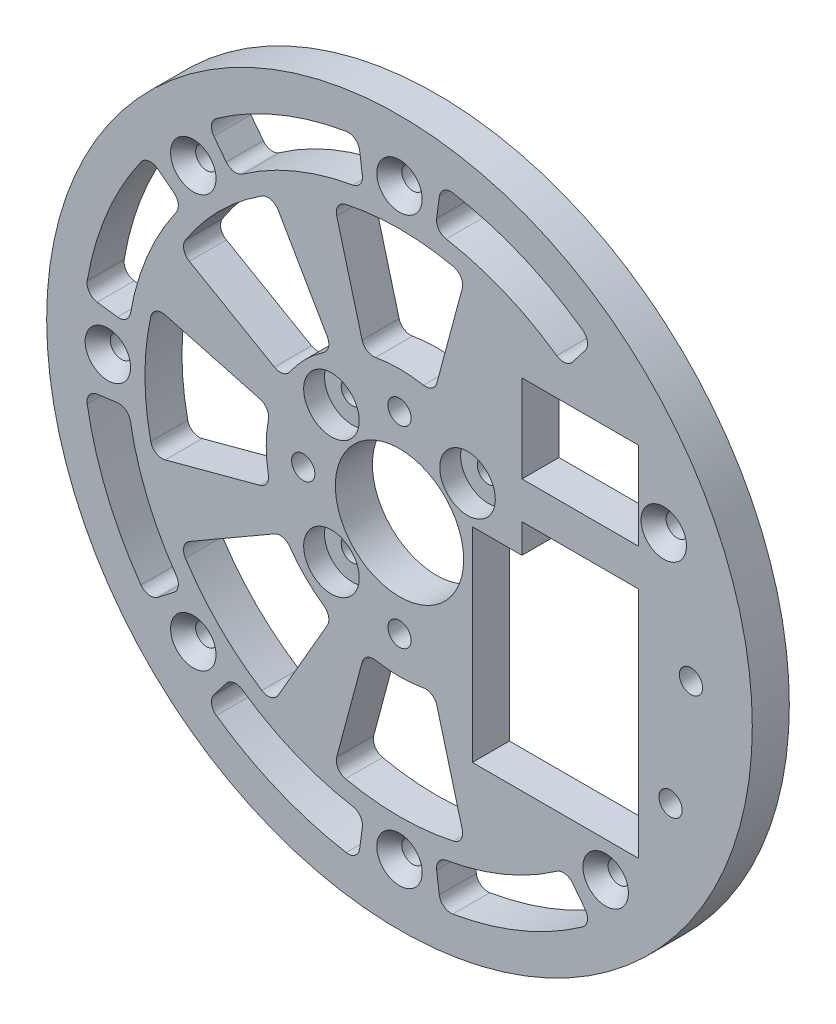
SolidWorks part; units mm, degrees
material "Balsa"
ref_plane "Front Plane" through (0, 0, 0) normal (0, 0, 1) x (1, 0, 0)
ref_plane "Top Plane" through (0, 0, 0) normal (0, 1, 0) x (1, 0, 0)
ref_plane "Right Plane" through (0, 0, 0) normal (1, 0, 0) x (0, 0, -1)
sketch "Sketch1" plane through (0, 0, 0) normal (0, 0, 1) x (1, 0, 0)
  line L0 (45.3154, 21.1309) -> (0, 0) construction
  line L1 (0, 0) -> (35.3553, -35.3553) construction
  line L2 (49.9788, 1.4542) -> (0, 0) construction
  line L3 (0, 0) -> (46.4674, -18.4603) construction
  circle A0 centre (45.3154, 21.1309) radius 1.8986
  circle A1 centre (49.9788, 1.4542) radius 1.9939
  circle A2 centre (0, 0) radius 60.5
  circle A3 centre (0, 0) radius 11
  circle A4 centre (0, 0) radius 16.5 construction
  circle A5 centre (46.4674, -18.4603) radius 1.9939
  circle A6 centre (0, 0) radius 50 construction
  circle A27 centre (0, -16.5) radius 1.9939
  circle A28 centre (11.6673, -11.6673) radius 1.8986 construction
  circle A30 centre (0, -50) radius 1.8986
  circle A31 centre (-16.5, 0) radius 1.9939
  circle A32 centre (-11.6673, -11.6673) radius 1.8986
  circle A33 centre (0, 16.5) radius 1.9939
  circle A34 centre (-11.6673, 11.6673) radius 1.8986
  circle A35 centre (16.5, 0) radius 1.9939 construction
  circle A36 centre (11.6673, 11.6673) radius 1.8986
  circle A38 centre (-35.3553, -35.3553) radius 1.8986
  circle A40 centre (-50, 0) radius 1.8986
  circle A42 centre (-35.3553, 35.3553) radius 1.8986
  circle A44 centre (0, 50) radius 1.8986
  circle A46 centre (35.3553, 35.3553) radius 1.8986 construction
  circle A48 centre (50, 0) radius 1.8986 construction
  circle A50 centre (35.3553, -35.3553) radius 1.8986
  point P72 (0, 0)
  dimension "D1" = 121
  dimension "D4" = 70
  dimension "D6" = 100
  dimension "D7" = 23.333
  dimension "D8" = 33
  dimension "D9" = 3.7973
  dimension "D10" = 3.9878
  dimension "D15" = 3.7973
  dimension "D17" = 3.9878
  dimension "D18" = 3.7973
  dimension "D3" = 22
  dimension "D11" = 3.9878
  dimension "D5" = 23.333
  dimension "D19" = 45
  dimension "D20" = 4
  dimension "D21" = 8
extrude "Boss-Extrude1" add sketch "Sketch1" along normal blind 6.35
sketch "Sketch2" plane through (0, 0, 0) normal (0, 0, 1) x (1, 0, 0)
  line L0 (12.5, -29.35) -> (41, -29.35)
  line L1 (41, -29.35) -> (41, 10.65)
  line L5 (41, 17) -> (41, 32)
  line L6 (41, 32) -> (21, 32)
  line L7 (21, 32) -> (21, 17)
  line L8 (21, 17) -> (41, 17)
  line L10 (41, 10.65) -> (21, 10.65)
  line L11 (21, 10.65) -> (21, 5.65)
  line L12 (21, 5.65) -> (12.5, 5.65)
  line L13 (12.5, 5.65) -> (12.5, -29.35)
  dimension "D1" = 20
  dimension "D2" = 6.35
  dimension "D3" = 40
  dimension "D4" = 15
  dimension "D6" = 5
  dimension "D8" = 8.5
  dimension "D9" = 21
  dimension "D10" = 32
extrude "Cut-Extrude1" cut sketch "Sketch2" along normal through all
sketch "Sketch3" plane through (0, 0, 6.35) normal (0, 0, 1) x (1, 0, 0)
  line L0 (0, 0) -> (-84.2283, 0) construction
  line L4 (-42.1627, -11.2975) -> (-22.0714, -5.914)
  line L5 (-22.0714, 5.914) -> (-42.1627, 11.2975)
  arc A0 (-42.1627, -11.2975) -> (-42.1627, 11.2975) centre (0, 0) cw
  arc A1 (-22.0714, -5.914) -> (-22.0714, 5.914) centre (0, 0) cw
  circle A2 centre (-16.5, 0) radius 1.9939 construction
  circle A4 centre (-50, 0) radius 1.8987 construction
  circle A5 centre (-50, 0) radius 1.8986 construction
  point P6 (-43.65, 0)
  point P7 (-22.85, 0)
  dimension "D1" = 6.35
  dimension "D3" = 30
  dimension "D2" = 6.35
extrude "Cut-Extrude2" cut sketch "Sketch3" against normal through all
fillet "Fillet1" radius 2 4 edges at (-42.1627, -11.2975, 3.175) (-22.0714, -5.914, 3.175) (-22.0714, 5.914, 3.175) (-42.1627, 11.2975, 3.175)
pattern_circular "CirPattern1" count 8 over 360 about axis through (0, 0, 0) along (0, 0, 1) skipping 3, 4, 5 of "Fillet1", "Cut-Extrude2"
sketch "Sketch4" plane through (0, 0, 6.35) normal (0, 0, 1) x (1, 0, 0)
  line L0 (-85.2293, 0) -> (0, 0) construction
  line L1 (0, 0) -> (-89.0309, 36.8778) construction
  line L2 (-43.0989, 33.071) -> (-37.1488, 28.5053)
  line L3 (-53.8602, 7.0908) -> (-46.4244, 6.1119)
  arc A0 (-46.4244, 6.1119) -> (-37.1488, 28.5053) centre (0, 0) cw
  arc A1 (-53.8602, 7.0908) -> (-43.0989, 33.071) centre (0, 0) cw
  circle A2 centre (-50, 0) radius 1.8987 construction
  circle A3 centre (-50, 0) radius 1.8986
  arc A4 (-42.6565, 9.2598) -> (-42.6565, -9.2598) centre (0, 0) ccw construction
  circle A5 centre (0, 0) radius 60.5 construction
  point P17 (-43.2607, 17.9192)
  dimension "D3" = 3.175
  dimension "D4" = 6.175
  dimension "D1" = 22.5
  dimension "D2" = 30
extrude "Cut-Extrude3" cut sketch "Sketch4" against normal through all
fillet "Fillet2" radius 2 4 edges at (-53.8602, 7.0908, 3.175) (-46.4244, 6.1119, 3.175) (-37.1488, 28.5053, 3.175) (-43.0989, 33.071, 3.175)
pattern_circular "CirPattern2" count 8 over 360 about axis through (0, 0, 0) along (0, 0, 1) skipping 3, 4 of "Fillet2", "Cut-Extrude3"
chamfer "Chamfer1" distance 2.301 angle 41 7 edges at (1.8986, 50, 6.35) (-33.4567, 35.3553, 6.35) (-48.1014, 0, 6.35) (-33.4567, -35.3553, 6.35) (1.8986, -50, 6.35) (37.254, -35.3553, 6.35) (47.214, 21.1309, 6.35)
sketch "Sketch5" plane through (0, 0, 6.35) normal (0, 0, 1) x (1, 0, 0)
  circle A0 centre (-11.6673, -11.6673) radius 1.8986 construction
  circle A1 centre (-11.6673, 11.6673) radius 1.8986 construction
  circle A2 centre (11.6673, 11.6673) radius 1.8986 construction
  circle A3 centre (-11.6673, -11.6673) radius 1.8986
  circle A4 centre (-11.6673, 11.6673) radius 1.8986
  circle A5 centre (11.6673, 11.6673) radius 1.8986
  circle A6 centre (11.6673, 11.6673) radius 4.7625
  circle A7 centre (-11.6673, 11.6673) radius 4.7625
  circle A8 centre (-11.6673, -11.6673) radius 4.7625
  dimension "D1" = 9.525
extrude "Cut-Extrude4" cut sketch "Sketch5" against normal blind 3.5719
